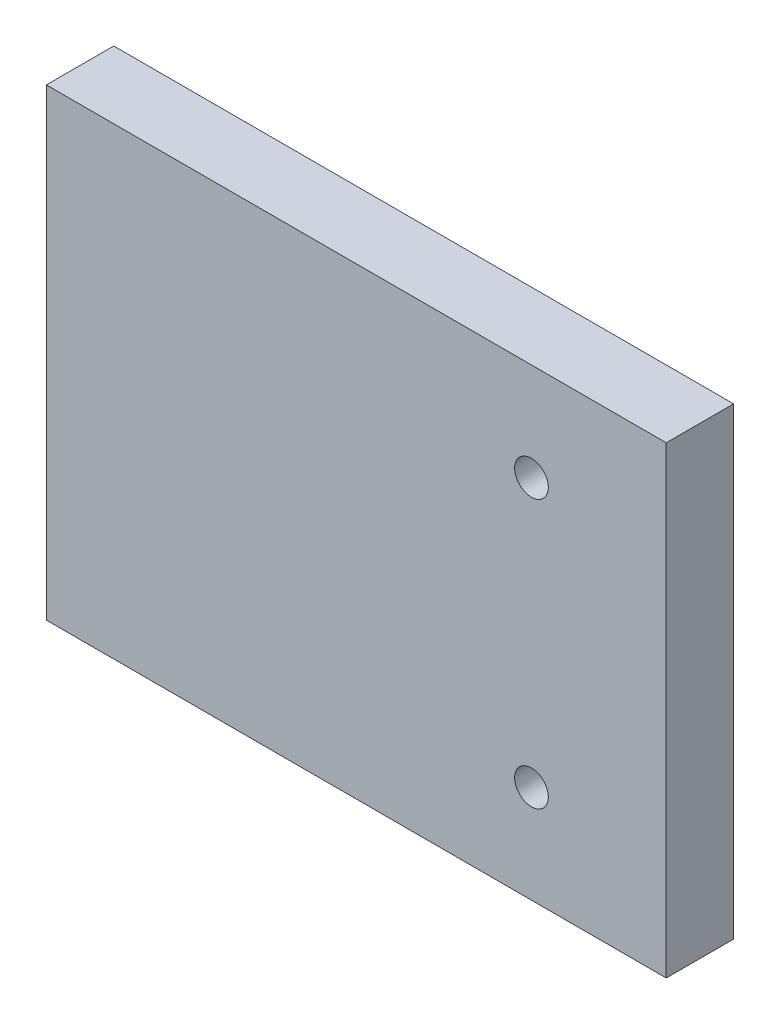
SolidWorks part; units mm, degrees
ref_plane "Front Plane" through (0, 0, 0) normal (0, 0, 1) x (1, 0, 0)
ref_plane "Top Plane" through (0, 0, 0) normal (0, 1, 0) x (1, 0, 0)
ref_plane "Right Plane" through (0, 0, 0) normal (1, 0, 0) x (0, 0, -1)
sketch "Sketch1" plane through (0, 0, 0) normal (0, 0, 1) x (1, 0, 0)
  line L0 (58.42, 21.844) -> (0, 21.844) construction
  line L1 (0, 0) -> (58.42, 0)
  line L2 (0, 0) -> (0, 43.688)
  line L3 (0, 43.688) -> (58.42, 43.688)
  line L4 (58.42, 0) -> (58.42, 43.688)
  circle A0 centre (45.72, 34.4805) radius 1.5875
  circle A1 centre (45.72, 9.2075) radius 1.5875
  dimension "D3" = 12.6365
  dimension "D4" = 3.175
  dimension "D1" = 43.688
  dimension "D2" = 58.42
  dimension "D5" = 12.7
extrude "Boss-Extrude1" add sketch "Sketch1" along normal blind 6.35
